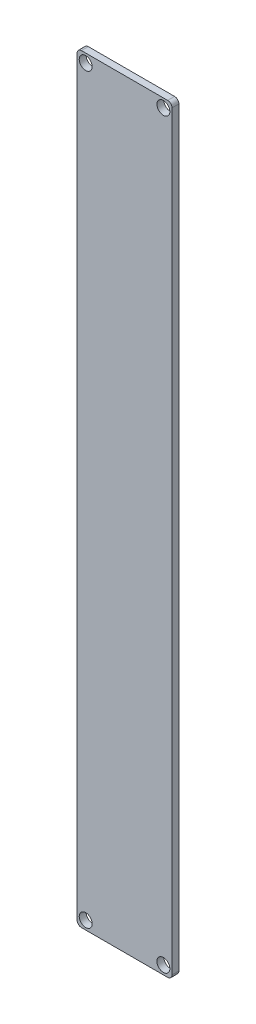
SolidWorks part; units mm, degrees
material "Power Circuit Board"
ref_plane "Front Plane" through (0, 0, 0) normal (0, 0, 1) x (1, 0, 0)
ref_plane "Top Plane" through (0, 0, 0) normal (0, 1, 0) x (1, 0, 0)
ref_plane "Right Plane" through (0, 0, 0) normal (1, 0, 0) x (0, 0, -1)
sketch "Sketch1" plane through (0, 0, 0) normal (0, 0, 1) x (1, 0, 0)
  line L1 (-35.5385, 79.3692) -> (-13.5385, 79.3692)
  line L2 (-35.5385, 79.3692) -> (-35.5385, -96.6308)
  line L3 (-35.5385, -96.6308) -> (-13.5385, -96.6308)
  line L4 (-13.5385, 79.3692) -> (-13.5385, -96.6308)
  dimension "D1" = 176
  dimension "D2" = 22
extrude "Boss-Extrude1" add sketch "Sketch1" along normal blind 1.6
sketch "Sketch2" plane through (0, 0, 1.6) normal (0, 0, 1) x (1, 0, 0)
  line L0 (-35.5385, 79.3692) -> (-35.5385, -96.6308) construction
  line L2 (-13.5385, 79.3692) -> (-35.5385, 79.3692) construction
  line L3 (-13.5385, -96.6308) -> (-13.5385, 79.3692) construction
  line L4 (-35.5385, -96.6308) -> (-13.5385, -96.6308) construction
  circle A0 centre (-33.5385, 77.3692) radius 1.5
  circle A1 centre (-15.5385, 77.3692) radius 1.5
  circle A2 centre (-33.5385, -94.6308) radius 1.5
  circle A3 centre (-15.5385, -94.6308) radius 1.5
  dimension "D1" = 3
  dimension "D2" = 3
  dimension "D3" = 3
  dimension "D4" = 3
  dimension "D5" = 2
  dimension "D6" = 2
  dimension "D7" = 2
  dimension "D8" = 2
  dimension "D9" = 2
  dimension "D10" = 2
  dimension "D11" = 2
  dimension "D12" = 2
extrude "Cut-Extrude1" cut sketch "Sketch2" against normal through all
fillet "Fillet1" radius 1 4 edges at (-35.5385, 79.3692, 0.8) (-13.5385, 79.3692, 0.8) (-13.5385, -96.6308, 0.8) (-35.5385, -96.6308, 0.8)
